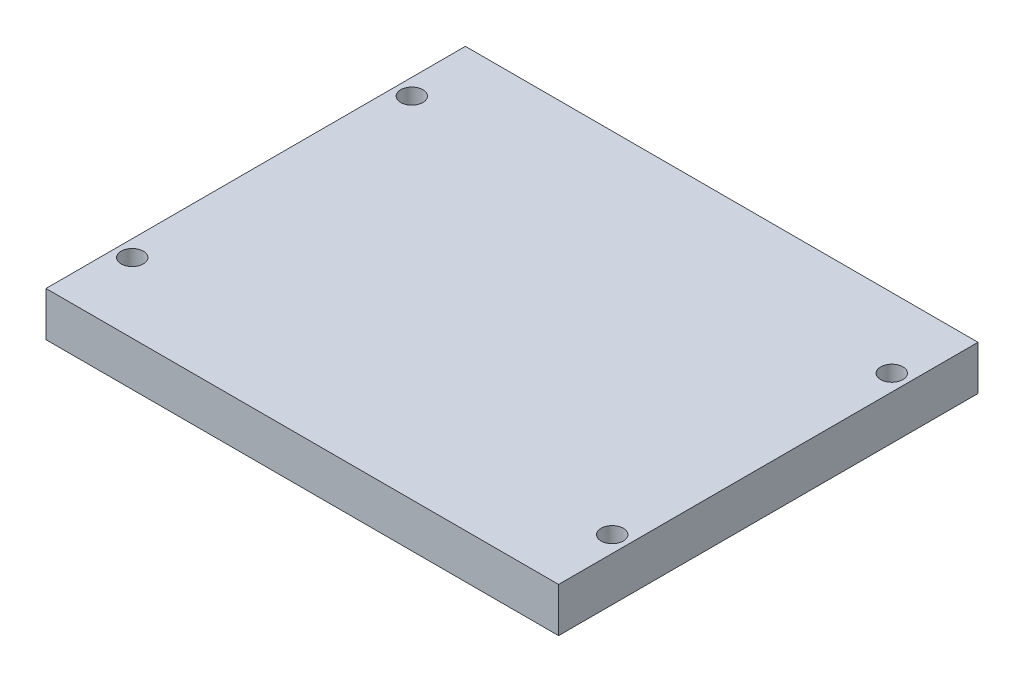
SolidWorks part; units mm, degrees
ref_plane "Front Plane" through (0, 0, 0) normal (0, 0, 1) x (1, 0, 0)
ref_plane "Top Plane" through (0, 0, 0) normal (0, 1, 0) x (1, 0, 0)
ref_plane "Right Plane" through (0, 0, 0) normal (1, 0, 0) x (0, 0, -1)
sketch "Sketch1" plane through (0, 0, 0) normal (0, 1, 0) x (1, 0, 0)
  line L1 (0, 0) -> (110, 0)
  line L2 (0, 0) -> (0, 90)
  line L3 (0, 90) -> (110, 90)
  line L4 (110, 0) -> (110, 90)
extrude "Boss-Extrude1" add sketch "Sketch1" along normal blind 9.525
sketch "Sketch2" plane through (0, 9.525, 0) normal (0, 1, 0) x (1, 0, 0)
  line L0 (110, 60.0666) -> (106.5, 60.0666) construction
  line L1 (110, 0) -> (110, 90) construction
  line L2 (106.5, 90) -> (106.5, 0) construction
  line L3 (110, 90) -> (0, 90) construction
  line L4 (0, 0) -> (110, 0) construction
  line L5 (3.5, 90) -> (3.5, 0) construction
  line L6 (106.5, 34.022) -> (3.5, 34.022) construction
  line L7 (110, 15) -> (0, 15) construction
  line L8 (0, 90) -> (0, 0) construction
  line L9 (110, 45) -> (0, 45) construction
  line L10 (110, 75) -> (0, 75) construction
  circle A0 centre (106.5, 15) radius 2.3813
  circle A1 centre (106.5, 45) radius 2.3813 construction
  circle A2 centre (106.5, 75) radius 2.3813
  circle A3 centre (3.5, 75) radius 2.3812
  circle A4 centre (3.5, 45) radius 2.3812 construction
  circle A5 centre (3.5, 15) radius 2.3813
extrude "Cut-Extrude1" cut sketch "Sketch2" against normal through all
